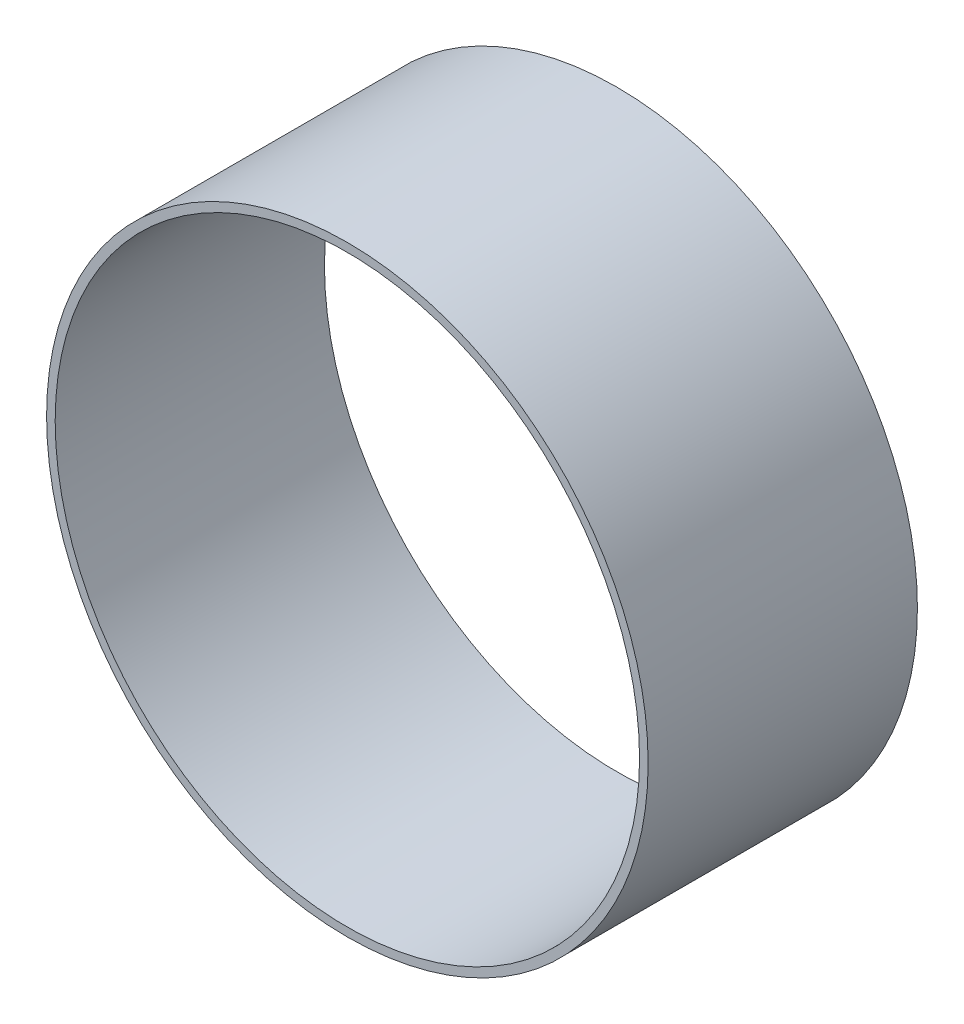
SolidWorks part; units mm, degrees
ref_plane "Front" through (0, 0, 0) normal (0, 0, 1) x (1, 0, 0)
ref_plane "Top" through (0, 0, 0) normal (0, 1, 0) x (1, 0, 0)
ref_plane "Right" through (0, 0, 0) normal (1, 0, 0) x (0, 0, -1)
sketch "Sketch1" plane through (0, 0, 0) normal (0, 0, 1) x (1, 0, 0)
  circle A0 centre (0, 0) radius 161.925
  circle A1 centre (0, 0) radius 166.6875
  dimension "D1" = 323.85
  dimension "D2" = 333.375
extrude "Boss-Extrude1" add sketch "Sketch1" along normal mid plane 149.225
